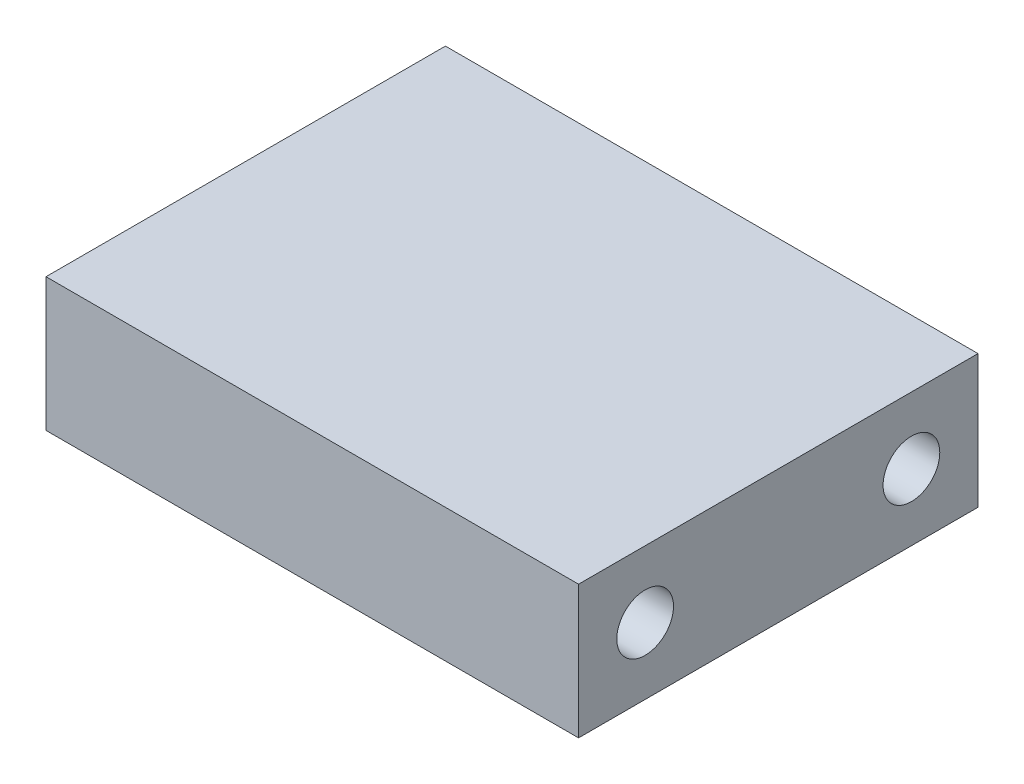
SolidWorks part; units mm, degrees
material "6061 Alloy"
ref_plane "Front Plane" through (0, 0, 0) normal (0, 0, 1) x (1, 0, 0)
ref_plane "Top Plane" through (0, 0, 0) normal (0, 1, 0) x (1, 0, 0)
ref_plane "Right Plane" through (0, 0, 0) normal (1, 0, 0) x (0, 0, -1)
sketch "Sketch1" plane through (0, 0, 0) normal (0, 1, 0) x (1, 0, 0)
  line L0 (-12.7, 0) -> (12.7, 0) construction
  line L1 (-12.7, 9.525) -> (12.7, 9.525)
  line L2 (-12.7, 9.525) -> (-12.7, -9.525)
  line L3 (-12.7, -9.525) -> (12.7, -9.525)
  line L4 (12.7, 9.525) -> (12.7, -9.525)
  line L6 (0, 9.525) -> (0, -9.525) construction
  dimension "D1" = 25.4
  dimension "D2" = 19.05
extrude "Extrude1" add sketch "Sketch1" along normal blind 6.35
hole_wizard "Tap Drill for #6 Tap1" positions "3DSketch1" profile "Sketch2" hole size "#6-32" standard "Ansi Inch"
sketch3d "3DSketch1"
  line L0 (12.7, 6.35, 9.525) -> (12.7, 6.35, -9.525) construction
  line L1 (12.7, 6.35, 9.525) -> (12.7, 0, 9.525) construction
  point P0 (12.7, 3.175, 6.35)
  point P2 (12.7, 3.175, -6.35)
  dimension "D1" = 3.175
  dimension "D2" = 12.7
  dimension "D3" = 3.175
sketch "Sketch2" plane through (12.7, 3.175, 6.35) normal (0, 1, 0) x (0, 0, -1)
  line L0 (0, 0) -> (0, 13.5127)
  line L1 (0, 13.5127) -> (1.3525, 12.7)
  line L2 (1.3525, 12.7) -> (1.3525, 0)
  line L5 (1.3525, 0) -> (0, 0)
  line L10 (0, 13.5127) -> (-1.3526, 12.7) construction
  line L11 (0, -6.35) -> (0, 107.95) construction
  dimension "Hole Dia." = 2.7051
  dimension "Hole Depth" = 12.7
  dimension "Drill Angle" = 118
